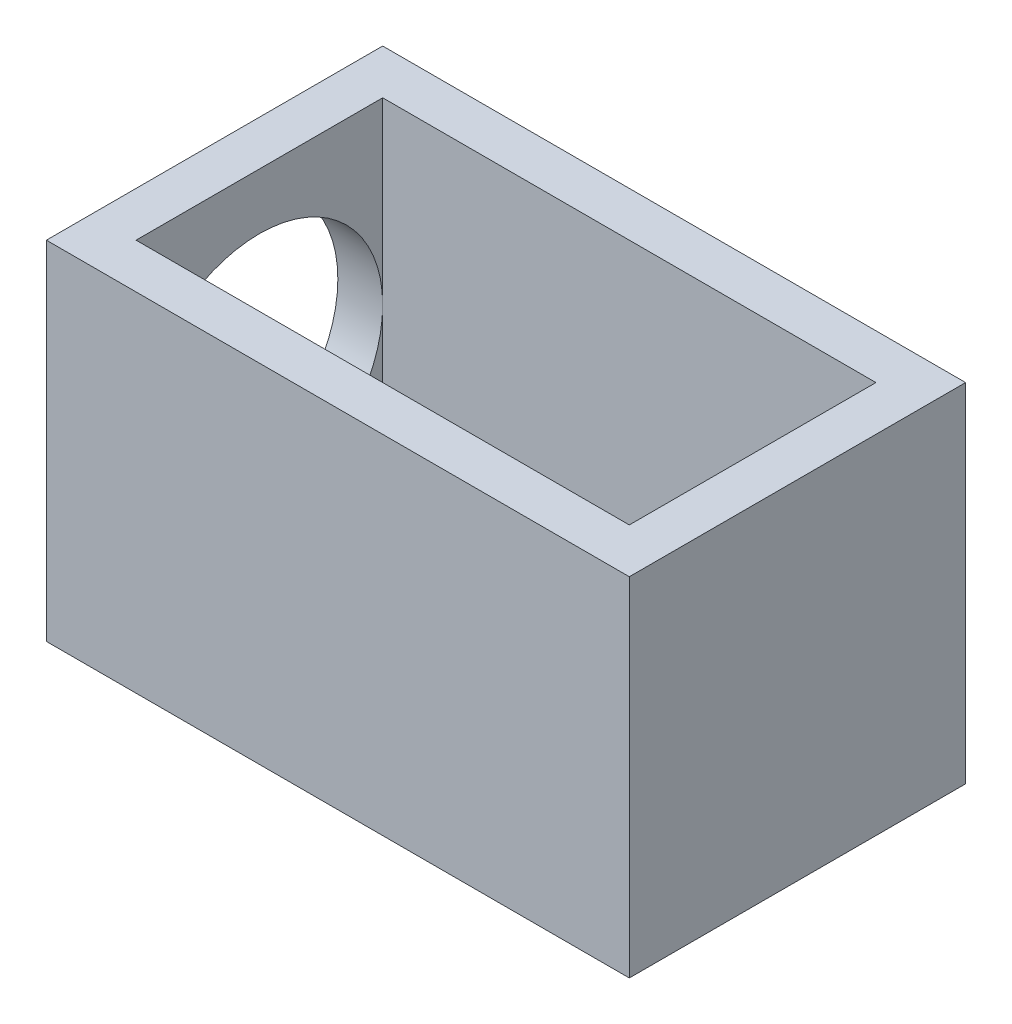
SolidWorks part; units mm, degrees
ref_plane "Front Plane" through (0, 0, 0) normal (0, 0, 1) x (1, 0, 0)
ref_plane "Top Plane" through (0, 0, 0) normal (0, 1, 0) x (1, 0, 0)
ref_plane "Right Plane" through (0, 0, 0) normal (1, 0, 0) x (0, 0, -1)
sketch "Sketch1" plane through (0, 0, 0) normal (0, 1, 0) x (1, 0, 0)
  line L0 (-6.5, 3.75) -> (6.5, 3.75)
  line L1 (-5.5, 2.75) -> (5.5, 2.75)
  line L2 (-5.5, 2.75) -> (-5.5, -2.75)
  line L3 (-5.5, -2.75) -> (5.5, -2.75)
  line L4 (5.5, 2.75) -> (5.5, -2.75)
  line L5 (-5.5, 2.75) -> (5.5, -2.75) construction
  line L6 (-5.5, -2.75) -> (5.5, 2.75) construction
  line L7 (6.5, 3.75) -> (6.5, -3.75)
  line L8 (-6.5, -3.75) -> (6.5, -3.75)
  line L9 (-6.5, 3.75) -> (-6.5, -3.75)
  point P0 (0, 0)
  dimension "D1" = 5.5
  dimension "D2" = 11
  dimension "D3" = 1
extrude "Boss-Extrude1" add sketch "Sketch1" along normal blind 7.75
sketch "Sketch2" plane through (-6.5, 0, 0) normal (-1, 0, 0) x (0, 0, 1)
  line L0 (-3.75, 7.75) -> (3.75, 7.75) construction
  line L1 (-3.75, 0) -> (3.75, 0) construction
  circle A0 centre (0, 3.75) radius 2.75
  point P4 (0, 0)
  point P6 (-10.4121, 8.5084)
  point P8 (0, 0)
  dimension "D1" = 5.5
  dimension "D2" = 4
extrude "Cut-Extrude1" cut sketch "Sketch2" against normal up to surface (1 mm away) up to face at (-5.5, 3.875, 0)
sketch "Sketch3" plane through (0, 0, 0) normal (0, -1, 0) x (1, 0, 0)
  line L1 (-6.5, -3.75) -> (6.5, -3.75)
  line L2 (-6.5, -3.75) -> (-6.5, 3.75)
  line L3 (-6.5, 3.75) -> (6.5, 3.75)
  line L4 (6.5, -3.75) -> (6.5, 3.75)
extrude "Boss-Extrude2" add sketch "Sketch3" against normal blind 1
sketch "Sketch4" plane through (0, 0, 0) normal (0, 0, 1) x (1, 0, 0)
  line L0 (2.25, 1) -> (5.5, 6.5)
  line L1 (5.5, 1) -> (-5.5, 1) construction
  line L2 (5.5, 6.5) -> (5.5, 1)
  line L3 (5.5, 1) -> (2.25, 1)
  line L4 (-5.5, 3.75) -> (-5.5, 1) construction
  point P9 (5.5, 6.6628)
  point P10 (5.5, 6.0031)
  dimension "D1" = 7.75
  dimension "D2" = 5.5
extrude "Boss-Extrude3" add sketch "Sketch4" along normal mid plane 6
